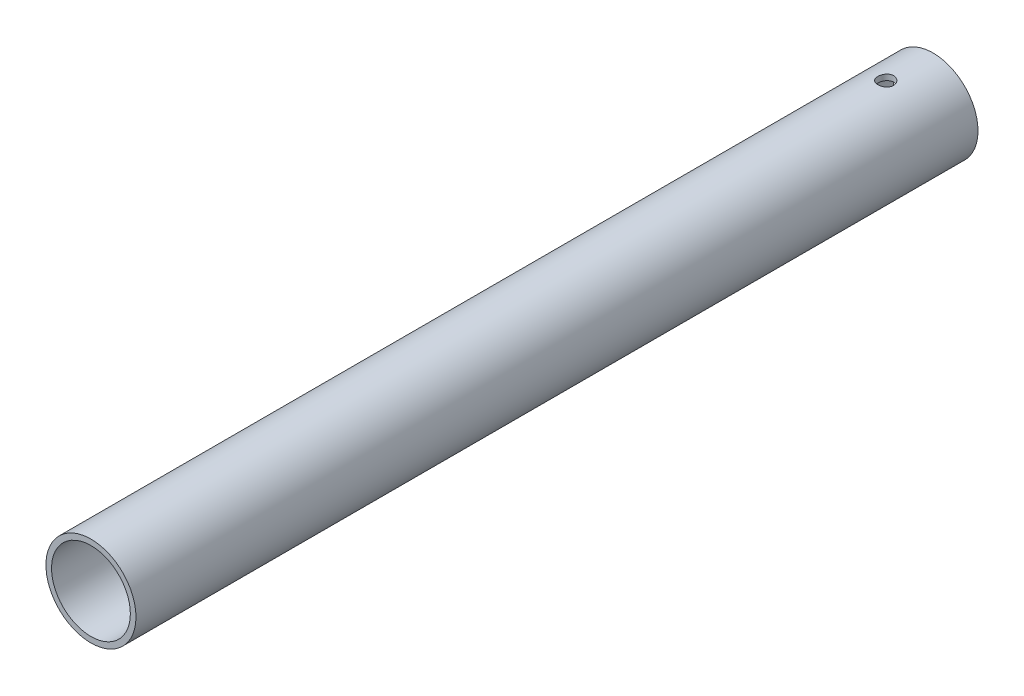
SolidWorks part; units mm, degrees
ref_plane "前基準面" through (0, 0, 0) normal (0, 0, 1) x (1, 0, 0)
ref_plane "上基準面" through (0, 0, 0) normal (0, 1, 0) x (1, 0, 0)
ref_plane "右基準面" through (0, 0, 0) normal (1, 0, 0) x (0, 0, -1)
sketch "草圖1" plane through (0, 0, 0) normal (0, 0, 1) x (1, 0, 0)
  circle A0 centre (0, 0) radius 8
  circle A1 centre (0, 0) radius 7
  dimension "D1" = 16
  dimension "D2" = 1
extrude "填料-伸長1" add sketch "草圖1" along normal blind 149.6
sketch "草圖2" plane through (0, 0, 0) normal (0, 1, 0) x (1, 0, 0)
  line L0 (0, -5.2608) -> (0, 5.2608) construction
  line L1 (7, 0) -> (-7, 0) construction
  circle A0 centre (0, -8.4) radius 1.4
  point P4 (0, 0)
  point P8 (0, 0)
  dimension "D1" = 2.8
  dimension "D2" = 8.4
extrude "除料-伸長1" cut sketch "草圖2" against normal through all both and the other way through all
